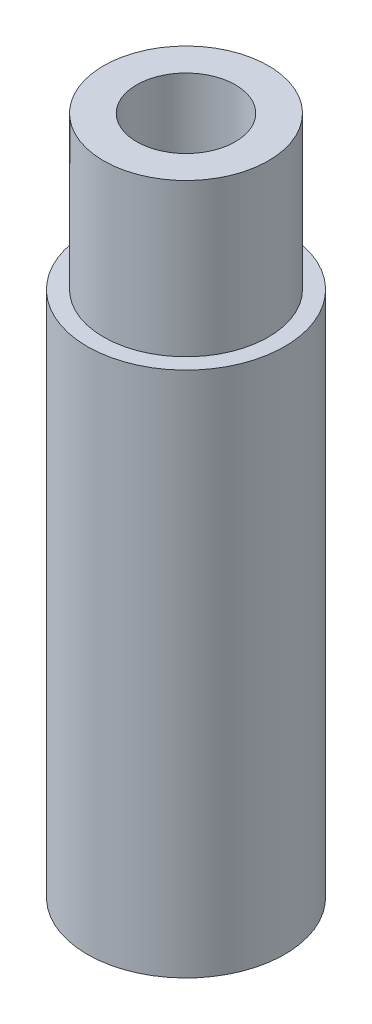
SolidWorks part; units mm, degrees
material "AISI 304"
ref_plane "Front Plane" through (0, 0, 0) normal (0, 0, 1) x (1, 0, 0)
ref_plane "Top Plane" through (0, 0, 0) normal (0, 1, 0) x (1, 0, 0)
ref_plane "Right Plane" through (0, 0, 0) normal (1, 0, 0) x (0, 0, -1)
sketch "Sketch1" plane through (0, 0, 0) normal (0, 1, 0) x (1, 0, 0)
  circle A0 centre (0, 0) radius 4.7625
  dimension "D1" = 9.525
extrude "Boss-Extrude1" add sketch "Sketch1" along normal blind 25.4
sketch "Sketch2" plane through (0, 25.4, 0) normal (0, 1, 0) x (1, 0, 0)
  circle A0 centre (0, 0) radius 3.9751
  dimension "D1" = 7.9502
extrude "Boss-Extrude2" add sketch "Sketch2" along normal blind 7.366
sketch "Sketch3" plane through (0, 0, 0) normal (0, -1, 0) x (1, 0, 0)
  circle A0 centre (0, 0) radius 2.3813
  dimension "D1" = 4.7625
extrude "Cut-Extrude1" cut sketch "Sketch3" against normal through all
sketch "Sketch4" plane through (0, 0, 0) normal (0, -1, 0) x (1, 0, 0)
  circle A0 centre (0, 0) radius 3.4544
  dimension "D1" = 6.9088
extrude "Cut-Extrude2" cut sketch "Sketch4" against normal blind 12.7
